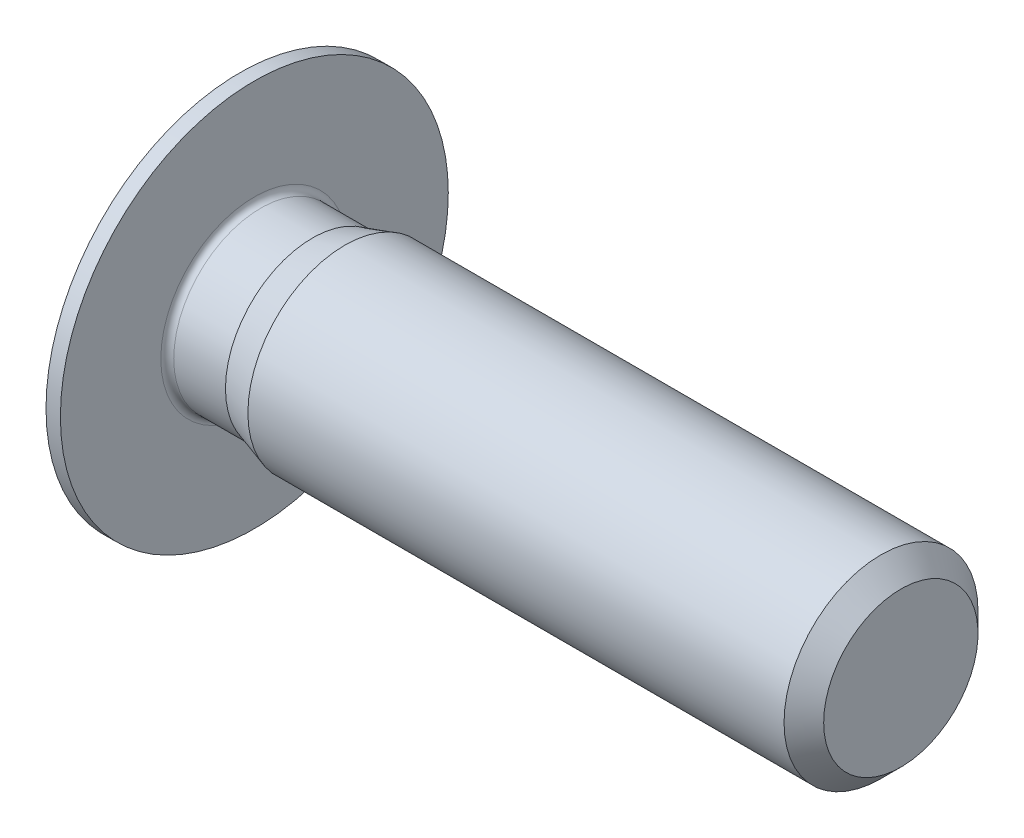
SolidWorks part; units mm, degrees
material "AISI 304"
ref_plane "正面" through (0, 0, 0) normal (0, 0, 1) x (1, 0, 0)
ref_plane "平面" through (0, 0, 0) normal (0, 1, 0) x (1, 0, 0)
ref_plane "右側面" through (0, 0, 0) normal (1, 0, 0) x (0, 0, -1)
ref_plane "Plane1" through (0, 0, 0) normal (0, 0, 1) x (1, 0, 0)
sketch "Sketch1" plane through (0, 0, 0) normal (0, 0, 1) x (1, 0, 0)
  line L0 (-0.8, 0) -> (-0.8, 2)
  line L1 (-0.8, 2) -> (-0.2226, 3)
  line L2 (-0.2226, 3) -> (0, 3)
  line L3 (0, 3) -> (0, 1.4467)
  line L4 (0.1, 1.3468) -> (0.9, 1.3468)
  line L5 (0.9, 1.3468) -> (1.4, 1.5)
  line L6 (1.4, 1.5) -> (9.6935, 1.5)
  line L7 (9.6935, 1.5) -> (10, 1.1935)
  line L8 (10, 1.1935) -> (10, 0)
  line L9 (10, 0) -> (-0.8, 0)
  line L10 (10, 0) -> (-0.8, 0) construction
  arc A0 (0, 1.4467) -> (0.1, 1.3468) centre (0.1, 1.4467) ccw
revolve "Revolve1" add sketch "Sketch1" angle 360 about L10
cosmetic thread "Cosmetic Thread1" parameters "D1"=8.6, "D2"=2.387
ref_plane "Plane2" through (0, 0, 0) normal (0, 0, 1) x (1, 0, 0)
sketch "Sketch2" plane through (0, 0, 0) normal (0, 0, 1) x (1, 0, 0)
  line L0 (-0.8, 0) -> (-0.8, 0.75)
  line L1 (-0.8, 0.75) -> (1.2, 0.75)
  line L2 (1.2, 0.75) -> (1.633, 0)
  line L3 (1.633, 0) -> (-0.8, 0)
  line L4 (1.633, 0) -> (-0.8, 0) construction
revolve "Cut-Revolve1" cut sketch "Sketch2" angle 360 about L4
ref_plane "Plane3" through (-0.8, 0, 0) normal (1, 0, 0) x (0, 0, -1)
sketch "Sketch3" plane through (-0.8, 0, 0) normal (1, 0, 0) x (0, 0, -1)
  line L0 (-0.75, -0.433) -> (0, -0.866)
  line L1 (0, -0.866) -> (0.75, -0.433)
  line L2 (0.75, -0.433) -> (0.75, 0.433)
  line L3 (0.75, 0.433) -> (0, 0.866)
  line L4 (0, 0.866) -> (-0.75, 0.433)
  line L5 (-0.75, 0.433) -> (-0.75, -0.433)
extrude "Cut-Extrude1" cut sketch "Sketch3" along normal blind 2
